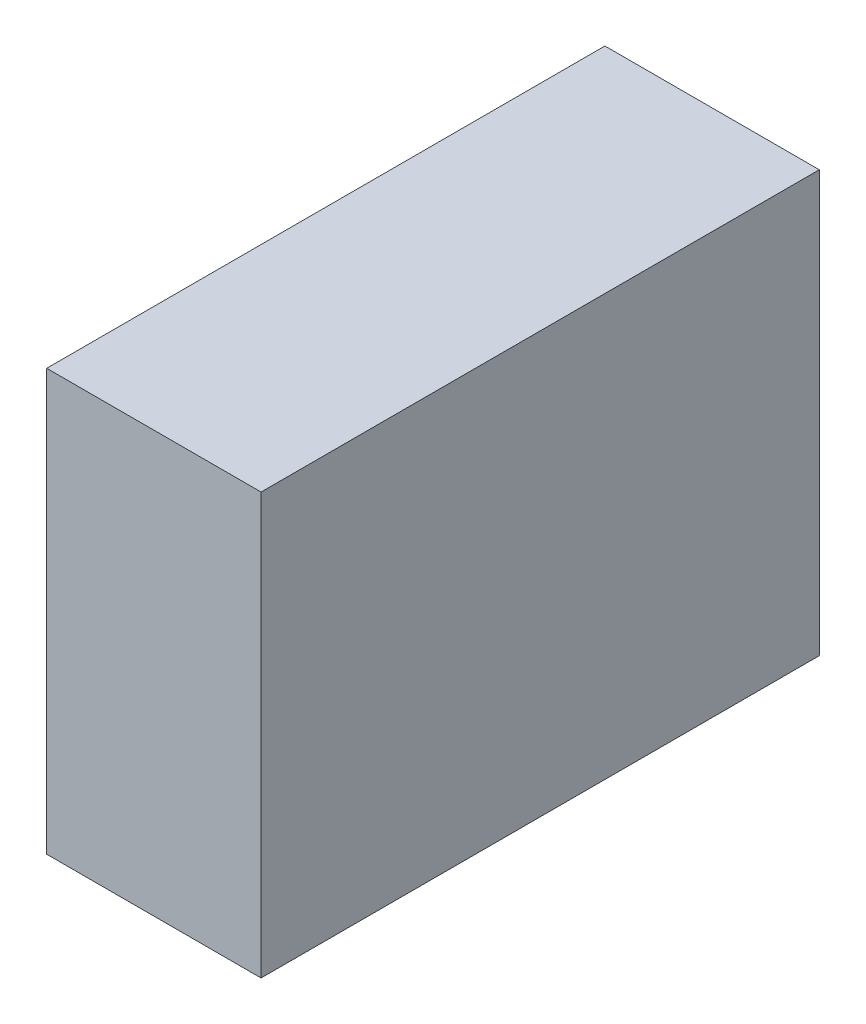
SolidWorks part; units mm, degrees
material "1023 al carbonio, lamiera (SS)"
ref_plane "Piano frontale" through (0, 0, 0) normal (0, 0, 1) x (1, 0, 0)
ref_plane "Piano superiore" through (0, 0, 0) normal (0, 1, 0) x (1, 0, 0)
ref_plane "Piano destro" through (0, 0, 0) normal (1, 0, 0) x (0, 0, -1)
sketch "Schizzo1" plane through (0, 0, 0) normal (0, 0, 1) x (1, 0, 0)
  line L0 (4.8, 18.849) -> (4.8, 0) construction
  line L1 (0, 0) -> (9.6, 0)
  line L2 (0, 0) -> (0, 18.849)
  line L3 (0, 18.849) -> (9.6, 18.849)
  line L4 (9.6, 0) -> (9.6, 18.849)
  dimension "D1" = 18.849
  dimension "D2" = 9.6
extrude "Estrusione-Estrusione1" add sketch "Schizzo1" along normal blind 25
